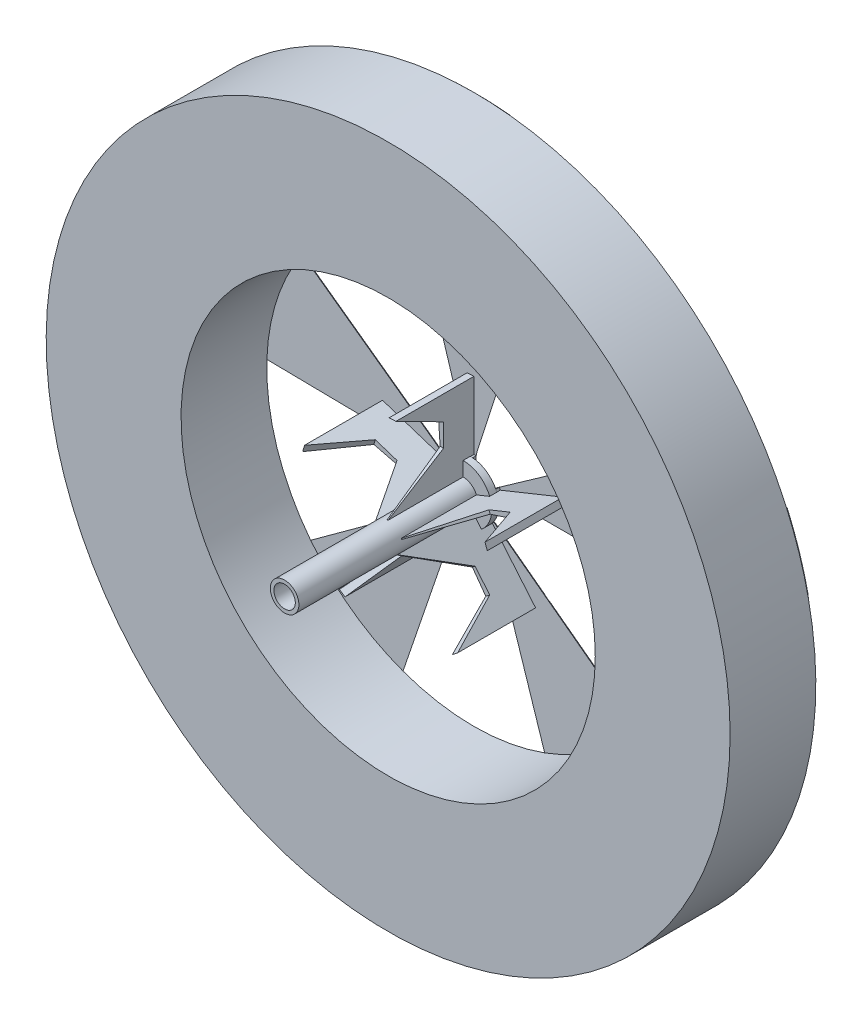
SolidWorks part; units mm, degrees
ref_plane "Front Plane" through (0, 0, 0) normal (0, 0, 1) x (1, 0, 0)
ref_plane "Top Plane" through (0, 0, 0) normal (0, 1, 0) x (1, 0, 0)
ref_plane "Right Plane" through (0, 0, 0) normal (1, 0, 0) x (0, 0, -1)
sketch "Esquisse1" plane through (0, 0, 0) normal (0, 0, 1) x (1, 0, 0)
  circle A0 centre (0, 0) radius 47.8814
  circle A1 centre (0, 0) radius 28.9989
extrude "Boss.-Extru.1" add sketch "Esquisse1" along normal blind 12
ref_plane "Plan1" through (0, 0, 0.5) normal (0, 0, 1) x (1, 0, 0)
sketch "Esquisse3" plane through (0, 0, 0.5) normal (0, 0, 1) x (1, 0, 0)
  circle A0 centre (0, 0) radius 4
extrude "Boss.-Extru.2" add sketch "Esquisse3" along normal blind 1 separate body
sketch "Esquisse4" plane through (0, 0, 0.5) normal (0, 0, -1) x (-1, 0, 0)
  circle A0 centre (0, 0) radius 2
  circle A1 centre (0, 0) radius 1.8
extrude "Enlèv. mat.-Extru.1" cut sketch "Esquisse4" against normal blind 0.2
sketch "Esquisse5" plane through (0, 0, 0) normal (0, 0, -1) x (-1, 0, 0)
  line L0 (0, 0) -> (0, 47.8814) construction
  line L1 (0, 0) -> (5, 47.6197) construction
  line L2 (0, 0) -> (-5, 47.6197) construction
  line L3 (5, 47.6197) -> (7.994, 27.8753) construction
  line L4 (7.994, 27.8753) -> (0.3192, 3.0401) construction
  line L5 (0.3192, 3.0401) -> (-0.3192, 3.0401) construction
  line L6 (-5, 47.6197) -> (-7.994, 27.8753) construction
  line L7 (-7.994, 27.8753) -> (-0.3192, 3.0401) construction
  line L8 (5, 47.6197) -> (7.994, 27.8753)
  line L9 (7.994, 27.8753) -> (0.3192, 3.0401)
  line L10 (0.3192, 3.0401) -> (-0.3192, 3.0401)
  line L11 (-0.3192, 3.0401) -> (-0.3192, 3.9872)
  line L12 (-0.3192, 3.9872) -> (-0.4903, 4.6691)
  line L13 (-0.4903, 4.6691) -> (-7.994, 27.8753)
  line L14 (-7.994, 27.8753) -> (-5, 47.6197)
  circle A0 centre (0, 0) radius 47.8814 construction
  circle A1 centre (0, 0) radius 28.9989 construction
  circle A2 centre (0, 0) radius 4 construction
  arc A3 (5, 47.6197) -> (-5, 47.6197) centre (0, 0) ccw
  point P15 (0, 3.0401)
  dimension "D1" = 10
extrude "Boss.-Extru.3" add sketch "Esquisse5" along normal blind 0.3 draft 45
sketch "Esquisse6" plane through (0, 0, 0) normal (0, 0, 1) x (1, 0, 0)
  line L0 (-0.3192, 3.0401) -> (0.3192, 3.0401)
  line L1 (-0.0979, 3.3401) -> (-0.3192, 3.0401) construction
  line L2 (-0.3192, 3.0401) -> (-7.994, 27.8753) construction
  line L3 (0.3192, 3.0401) -> (0.3192, 3.9872)
  line L4 (0.3192, 3.9872) -> (-0.6018, 3.9545)
  line L5 (-0.6018, 3.9545) -> (-0.3192, 3.0401)
  circle A0 centre (0, 0) radius 4 construction
extrude "Boss.-Extru.4" add sketch "Esquisse6" along normal up to next
sketch "Esquisse7" plane through (0, 0, -0.3) normal (0, 0, -1) x (-1, 0, 0)
  circle A0 centre (0.0338, 3.7332) radius 0.5447
extrude "Enlèv. mat.-Extru.3" cut sketch "Esquisse7" against normal blind 0.1
sketch "Esquisse10" plane through (0, 0, -0.3) normal (0, 0, -1) x (-1, 0, 0)
  line L0 (-0.2017, 4.7519) -> (-0.8765, 4.7519)
  line L1 (-0.8765, 4.7519) -> (1.4091, 12.4716)
  line L2 (1.4091, 12.4716) -> (0, 47.5814)
  line L3 (1.9173, 11.909) -> (0.4857, 47.579)
  line L4 (1.9173, 11.909) -> (-0.2017, 4.7519)
  arc A0 (4.7382, 47.3449) -> (-4.7382, 47.3449) centre (0, 0) ccw construction
  arc A1 (0, 47.5814) -> (0.4857, 47.579) centre (0.3128, 61.2779) ccw
extrude "Enlèv. mat.-Extru.4" cut sketch "Esquisse10" against normal blind 0.1
sketch "Esquisse11" plane through (0, 0, -0.3) normal (0, 0, -1) x (-1, 0, 0)
  line L0 (0.6216, 13.5449) -> (2.7317, 12.1964)
  line L1 (2.7317, 12.1964) -> (3.5296, 13.0801)
  arc A0 (0.6216, 13.5449) -> (3.5296, 13.0801) centre (0.239, 1.8228) cw
extrude "Enlèv. mat.-Extru.5" cut sketch "Esquisse11" against normal blind 0.1
pattern_circular "Répétition circulaire1" count 5 over 360 about axis through (0, 0, 0) along (0, 0, 1) of "Enlèv. mat.-Extru.5", "Enlèv. mat.-Extru.4", "Enlèv. mat.-Extru.3", "Boss.-Extru.4", "Boss.-Extru.3"
sketch "Esquisse12" plane through (0, 0, 1.5) normal (0, 0, 1) x (1, 0, 0)
  circle A0 centre (0, 0) radius 2
  circle A1 centre (0, 0) radius 1.5
extrude "Boss.-Extru.5" add sketch "Esquisse12" along normal blind 25
sketch "Esquisse16" plane through (0, 0, 0) normal (1, 0, 0) x (0, 0, -1)
  line L0 (-4.2414, 6.8515) -> (-12, 2)
  line L3 (-4.2414, 6.8515) -> (-4.2414, 10.0555)
  line L4 (-4.2414, 10.0555) -> (-10.9131, 13.4474)
  line L5 (-10.9131, 13.4474) -> (0, 13.4474)
  line L6 (0, 13.4474) -> (0, 2)
  line L8 (-12, 2) -> (0, 2)
  line L9 (0, 0) -> (-12, 0) construction
  line L10 (-12, 28.9989) -> (-12, -28.9989) construction
  line L11 (-12, 47.8814) -> (-12, -47.8814) construction
  line L12 (-1.5, 2) -> (-26.5, 2) construction
  line L13 (0, 19.4706) -> (0, 9.96) construction
revolve "Révolution1" add sketch "Esquisse16" angle 4 about L9
pattern_circular "Répétition circulaire2" count 5 over 360 about axis through (0, 0, 0) along (0, 0, 1) of "Révolution1"
sketch "Esquisse17" plane through (0, 0, 0.5) normal (0, 0, -1) x (-1, 0, 0)
  circle A0 centre (0, 0) radius 2
  circle A1 centre (0, 0) radius 3.0475
extrude "Enlèv. mat.-Extru.6" cut sketch "Esquisse17" along normal blind 25
